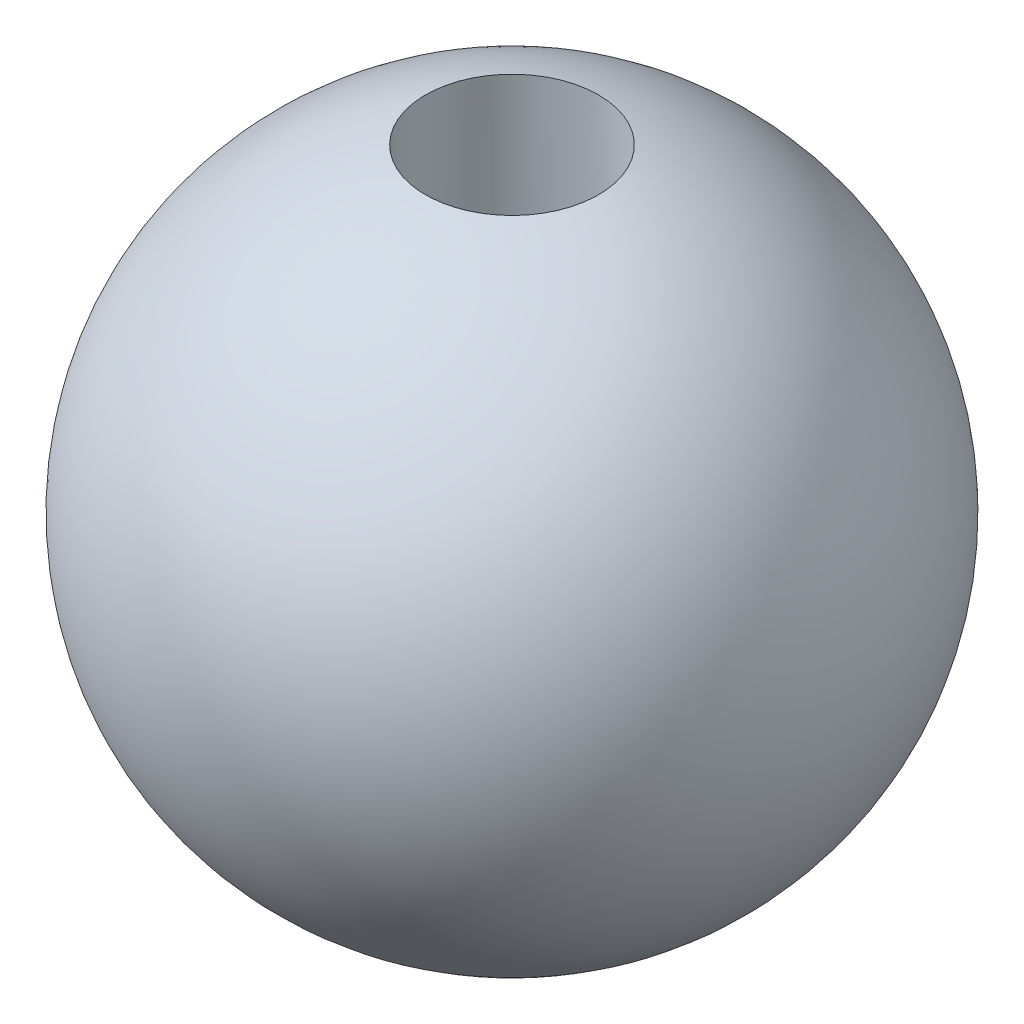
SolidWorks part; units mm, degrees
ref_plane "Front Plane" through (0, 0, 0) normal (0, 0, 1) x (1, 0, 0)
ref_plane "Top Plane" through (0, 0, 0) normal (0, 1, 0) x (1, 0, 0)
ref_plane "Right Plane" through (0, 0, 0) normal (1, 0, 0) x (0, 0, -1)
sketch "Sketch2" plane through (0, 0, 0) normal (0, 0, 1) x (1, 0, 0)
  line L0 (0, 0) -> (32.5, 0)
  arc A0 (0, 0) -> (32.5, 0) centre (16.25, 0) cw
  dimension "D1" = 32.5
revolve "Revolve1" add sketch "Sketch2" angle 360 about L0
ref_plane "Plane2" through (0, 16.25, 0) normal (0, 1, 0) x (1, 0, 0)
ref_plane "Plane4" through (0, 0, 0) normal (0, 1, 0) x (1, 0, 0)
sketch "Sketch3" plane through (0, 16.25, 0) normal (0, 1, 0) x (1, 0, 0)
  line L0 (0, 0) -> (32.5, 0) construction
  line L1 (16.25, 16.25) -> (16.25, -16.25) construction
  circle A0 centre (16.25, 0) radius 16.25 construction
  circle A1 centre (16.25, 0) radius 4.25
  dimension "D1" = 8.5
sketch "Sketch4" plane through (0, 0, 0) normal (0, 1, 0) x (1, 0, 0)
  line L0 (0, 0) -> (32.5, 0) construction
  line L1 (16.25, 16.25) -> (16.25, -16.25) construction
  circle A0 centre (16.25, 0) radius 4.75
  dimension "D1" = 9.5
loft "Cut-Loft1" cut profiles "Sketch4", "Sketch3"
ref_plane "Plane5" through (0, -17, 0) normal (0, 1, 0) x (1, 0, 0)
sketch "Sketch7" plane through (0, -17, 0) normal (0, 1, 0) x (1, 0, 0)
  circle A0 centre (16.25, 0) radius 5
  dimension "D1" = 10
extrude "Cut-Extrude4" cut sketch "Sketch7" along normal blind 3
sketch "Sketch8" plane through (0, -14, 0) normal (0, -1, 0) x (1, 0, 0)
  circle A0 centre (16.25, 0) radius 3
  dimension "D1" = 6
extrude "Cut-Extrude5" cut sketch "Sketch8" against normal blind 2.5
sketch "Sketch9" plane through (0, -11.5, 0) normal (0, -1, 0) x (1, 0, 0)
  line L0 (16.25, 0) -> (16.25, -3) construction
  line L1 (14.25, 2.2361) -> (14.25, -2.2361)
  line L2 (18.25, 2.2361) -> (18.25, -2.2361)
  circle A0 centre (16.25, 0) radius 3 construction
  arc A1 (14.25, -2.2361) -> (18.25, -2.2361) centre (16.25, 0) ccw
  arc A2 (18.25, 2.2361) -> (14.25, 2.2361) centre (16.25, 0) ccw
  dimension "D1" = 4
extrude "Cut-Extrude6" cut sketch "Sketch9" against normal blind 7
